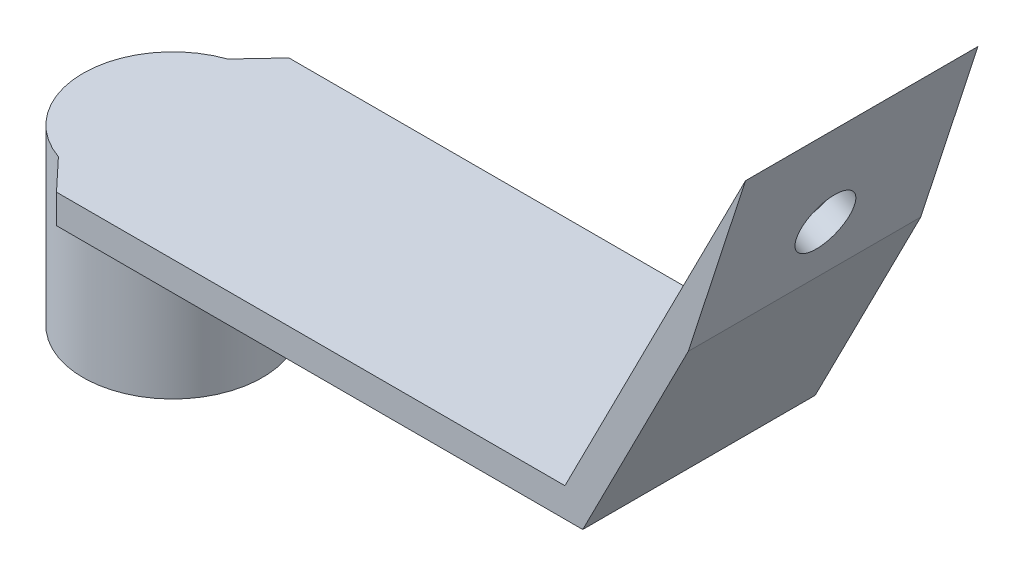
SolidWorks part; units mm, degrees
ref_plane "Front" through (0, 0, 0) normal (0, 0, 1) x (1, 0, 0)
ref_plane "Top" through (0, 0, 0) normal (0, 1, 0) x (1, 0, 0)
ref_plane "Right" through (0, 0, 0) normal (1, 0, 0) x (0, 0, -1)
sketch "Sketch1" plane through (0, 0, 0) normal (0, 0, 1) x (1, 0, 0)
  line L0 (-76.4958, -3.4222) -> (-20.9415, -3.4222)
  line L1 (-20.9415, -3.4222) -> (-1.2089, 35.3052)
  line L3 (-76.4958, -6.5972) -> (-18.9958, -6.5972)
  line L6 (-76.4958, -3.4222) -> (-76.4958, -6.5972)
  line L8 (-7.4645, 16.0344) -> (-1.2089, 35.3052)
  line L9 (-1.2089, 35.3052) -> (23.8053, 30.1317) construction
  line L10 (0.5203, 31.7054) -> (23.1623, 27.0225) construction
  line L11 (-18.9958, -6.5972) -> (-7.4645, 16.0344)
  line L12 (-18.9958, -6.5972) -> (0.5203, 31.7054) construction
  dimension "D2" = 57.5
  dimension "D3" = 25.4
  dimension "D4" = 117
  dimension "D1" = 3.175
extrude "Boss-Extrude1" add sketch "Sketch1" along normal blind 25.4
sketch "Sketch2" plane through (0, -3.4222, 0) normal (0, 1, 0) x (1, 0, 0)
  line L0 (-76.4958, -25.4) -> (-76.4958, 0) construction
  circle A0 centre (-76.4958, -12.7) radius 7.0714
  circle A1 centre (-76.4958, -12.7) radius 9.8014
extrude "Boss-Extrude2" add sketch "Sketch2" against normal blind 19
sketch "Sketch3" plane through (0, -3.4222, 0) normal (0, 1, 0) x (1, 0, 0)
  line L0 (-76.4958, 0) -> (-85.9296, -10.0406)
  line L1 (-85.9296, -10.0406) -> (-85.9296, -15.3594)
  line L2 (-85.9296, -15.3594) -> (-76.4958, -25.4)
  line L3 (-76.4958, 0) -> (-76.4958, -25.4)
  line L4 (-85.9296, -10.0406) -> (-86.2973, -12.7)
  line L5 (-86.2973, -12.7) -> (-85.9296, -15.3594)
  arc A0 (-76.4958, -2.8986) -> (-76.4958, -22.5014) centre (-76.4958, -12.7) ccw construction
  line M1 (-76.4958, 0) -> (-76.4958, -2.8986)
  arc M2 (-76.4958, -2.8986) -> (-76.4958, -22.5014) centre (-76.4958, -12.7) ccw
  line M3 (-76.4958, -22.5014) -> (-76.4958, -25.4)
  arc M7 (-76.4958, -19.7714) -> (-76.4958, -5.6286) centre (-76.4958, -12.7) cw
  line M8 (-76.4958, -5.6286) -> (-76.4958, -19.7714)
extrude "Boss-Extrude3" add sketch "Sketch3" against normal blind 3.175 contours L1 M7 | L4 L5 L1 M7 | L3 L1 M7 M2 | L2 M2 M3 | L1 M7 M8 | L3 L1 M2 M7 | L0 M1 M2
sketch "Sketch4" plane through (-15.241, 7.7657, 0) normal (-0.891, 0.454, 0) x (0, 0, 1)
  line L0 (25.4, 30.9084) -> (25.4, -12.5564) construction
  line L1 (25.4, 30.9084) -> (0, 30.9084) construction
  circle A0 centre (12.7, 18.2084) radius 3.175
  dimension "D1" = 6.35
  dimension "D2" = 12.7
  dimension "D3" = 12.7
extrude "Cut-Extrude1" cut sketch "Sketch4" against normal blind 3.175
